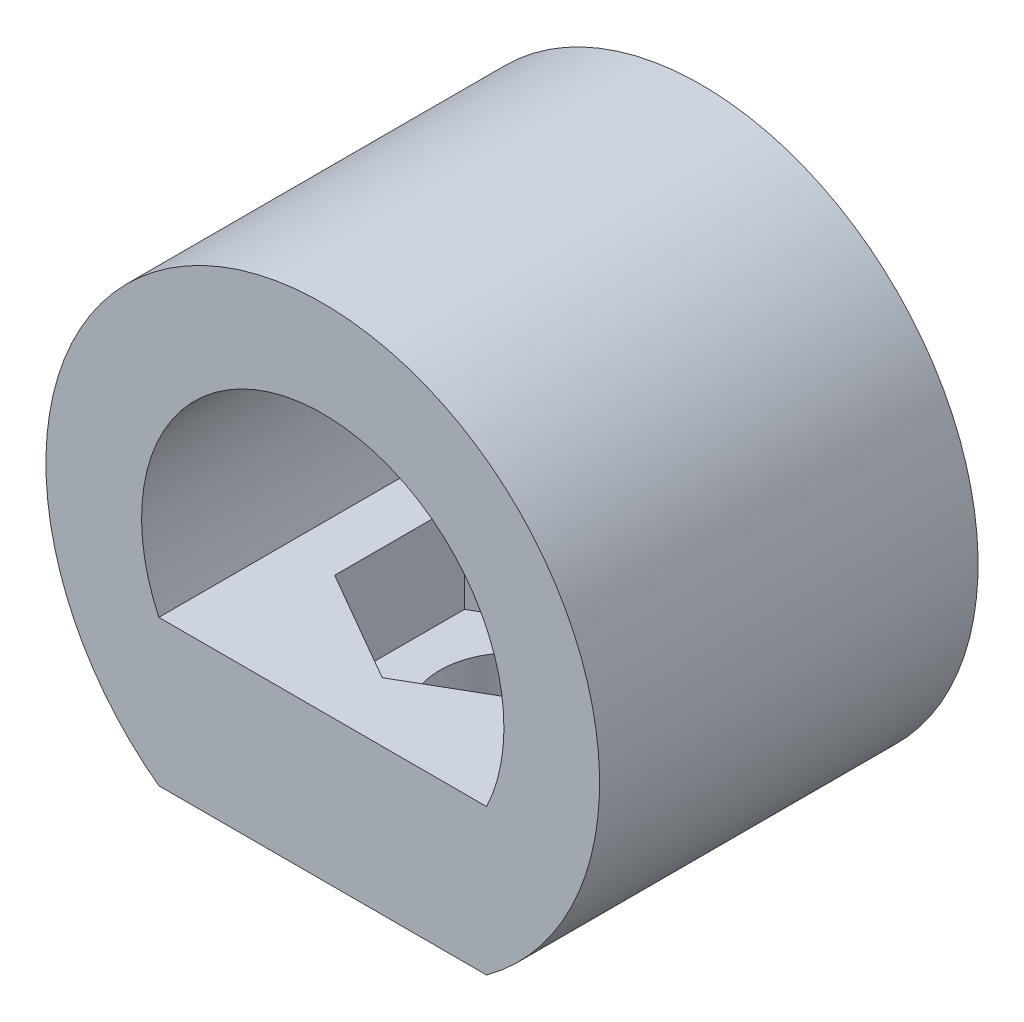
SolidWorks part; units mm, degrees
ref_plane "Plan de face" through (0, 0, 0) normal (0, 0, 1) x (1, 0, 0)
ref_plane "Plan de dessus" through (0, 0, 0) normal (0, 1, 0) x (1, 0, 0)
ref_plane "Plan de droite" through (0, 0, 0) normal (1, 0, 0) x (0, 0, -1)
sketch "Esquisse1" plane through (0, 0, 0) normal (0, 1, 0) x (1, 0, 0)
  line L0 (6.55, 0) -> (0, 0) construction
  line L1 (6.55, -3.7816) -> (6.55, 3.7816)
  line L2 (6.55, 3.7816) -> (0, 7.5633)
  line L3 (0, 7.5633) -> (-6.55, 3.7816)
  line L4 (-6.55, 3.7816) -> (-6.55, -3.7816)
  line L5 (-6.55, -3.7816) -> (0, -7.5633)
  line L6 (0, -7.5633) -> (6.55, -3.7816)
  line L7 (9.55, -5.5137) -> (9.55, 5.5137)
  line L8 (9.55, 5.5137) -> (0, 11.0274)
  line L9 (0, 11.0274) -> (-9.55, 5.5137)
  line L10 (-9.55, 5.5137) -> (-9.55, -5.5137)
  line L11 (-9.55, -5.5137) -> (0, -11.0274)
  line L12 (0, -11.0274) -> (9.55, -5.5137)
  line L14 (-9.55, -11.0274) -> (9.55, -11.0274)
  line L15 (-9.55, -11.0274) -> (-9.55, 11.0274)
  line L16 (-9.55, 11.0274) -> (9.55, 11.0274)
  line L17 (9.55, -11.0274) -> (9.55, 11.0274)
  circle A0 centre (0, 0) radius 6.55 construction
  point P20 (0, 0)
  dimension "D1" = 13.1
  dimension "D2" = 3
  dimension "D3" = 11.0274
extrude "Boss.-Extru.1" add sketch "Esquisse1" along normal blind 5.5 contours L11 L12 L7 L8 L9 L10 L6 L5 L4 L3 L2 L1 | L15 L14 L11 | L16 L15 L9 | L8 L17 L16 | L14 L17 L12
sketch "Esquisse5" plane through (0, 0, 0) normal (0, -1, 0) x (-1, 0, 0)
  line L1 (9.55, -11.0274) -> (-9.55, -11.0274)
  line L2 (9.55, -11.0274) -> (9.55, 11.0274)
  line L3 (9.55, 11.0274) -> (-9.55, 11.0274)
  line L4 (-9.55, -11.0274) -> (-9.55, 11.0274)
  circle A0 centre (0, 0) radius 4.2
  dimension "D1" = 8.4
extrude "Boss.-Extru.7" add sketch "Esquisse5" along normal blind 3
sketch "Esquisse6" plane through (0, 0, 0) normal (0, 0, 1) x (1, 0, 0)
  line L0 (0, 0) -> (0, 26.3622) construction
  line L2 (-9.55, -3) -> (9.55, -3)
  line L3 (-9.55, -3) -> (-9.55, 5.5)
  line L4 (-9.55, 5.5) -> (9.55, 5.5)
  line L5 (9.55, -3) -> (9.55, 5.5)
  circle A0 centre (0, 10) radius 10.5571
  circle A1 centre (0, 10) radius 16.1308
  dimension "D1" = 13
extrude "Boss.-Extru.8" add sketch "Esquisse6" along normal up to surface and the other way up to surface contours A0 L0 A1 L3 | L0 A0 L5 A1
